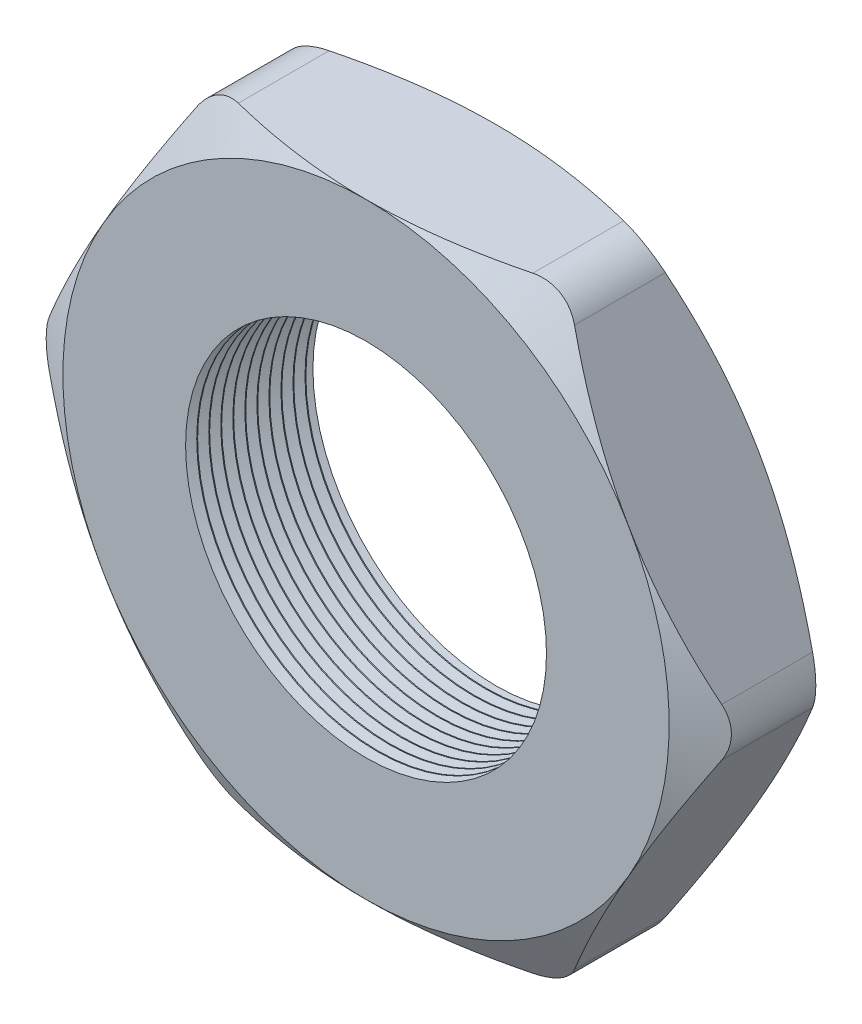
SolidWorks part; units mm, degrees
ref_plane "Front Plane" through (0, 0, 0) normal (0, 0, 1) x (1, 0, 0)
ref_plane "Top Plane" through (0, 0, 0) normal (0, 1, 0) x (1, 0, 0)
ref_plane "Right Plane" through (0, 0, 0) normal (1, 0, 0) x (0, 0, -1)
sketch "Sketch1" plane through (0, 0, 0) normal (0, 0, 1) x (1, 0, 0)
  line L1 (-18.4775, 0) -> (-9.2388, -16.002)
  line L2 (-9.2388, -16.002) -> (9.2388, -16.002)
  line L3 (9.2388, -16.002) -> (18.4775, 0)
  line L4 (18.4775, 0) -> (9.2388, 16.002)
  line L5 (9.2388, 16.002) -> (-9.2388, 16.002)
  line L6 (-9.2388, 16.002) -> (-18.4775, 0)
  circle A0 centre (0, 0) radius 16.002 construction
  circle A1 centre (0, 0) radius 9.525
  dimension "TS" = 19.05
  dimension "H" = 32.004
extrude "Extrude1" add sketch "Sketch1" along normal blind 6.858
sketch "Sketch2" plane through (0, 0, 6.858) normal (0, 0, 1) x (1, 0, 0)
  line L0 (9.2388, 16.002) -> (-9.2388, 16.002) construction
  circle A0 centre (0, 0) radius 16.002
extrude "Cut-Extrude1" cut sketch "Sketch2" against normal through all draft 60 flip side to cut
sketch "Sketch3" plane through (0, 0, 0) normal (0, 0, -1) x (-1, 0, 0)
  line L0 (-9.2388, 16.002) -> (9.2388, 16.002) construction
  circle A0 centre (0, 0) radius 16.002
extrude "Cut-Extrude2" cut sketch "Sketch3" against normal through all draft 60 flip side to cut
fillet "Fillet1" radius 2.54 6 edges at (18.4775, 0, 3.429) (9.2388, -16.002, 3.429) (-9.2388, -16.002, 3.429) (-18.4775, 0, 3.429) (-9.2388, 16.002, 3.429) (9.2388, 16.002, 3.429)
sketch "Sketch4" plane through (0, 0, 0) normal (0, 1, 0) x (1, 0, 0)
  line L0 (-9.525, -6.858) -> (-9.525, -6.2714)
  line L1 (-9.525, 0) -> (-9.525, -6.858) construction
  line L2 (-9.525, -6.2714) -> (-10.033, -6.5647)
  line L3 (-10.033, -6.5647) -> (-9.525, -6.858)
  dimension "D1" = 60
  dimension "D2" = 60
  dimension "D3" = 0.508
revolve "Cut-Revolve1" cut sketch "Sketch4" angle 360 about axis through (0, 0, 0) along (0, 0, 1)
pattern_linear "LPattern1" count 11 spacing 0.635 along (0, 0, -1) of "Cut-Revolve1"
